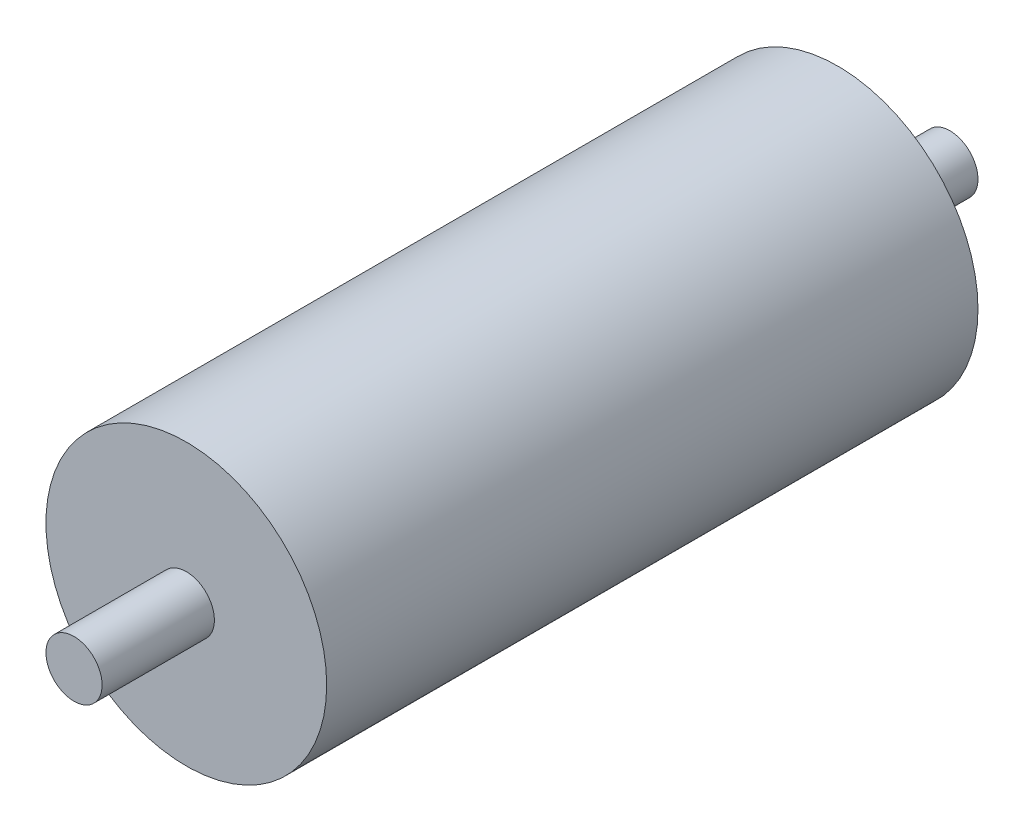
SolidWorks part; units mm, degrees
ref_plane "Front Plane" through (0, 0, 0) normal (0, 0, 1) x (1, 0, 0)
ref_plane "Top Plane" through (0, 0, 0) normal (0, 1, 0) x (1, 0, 0)
ref_plane "Right Plane" through (0, 0, 0) normal (1, 0, 0) x (0, 0, -1)
sketch "Sketch1" plane through (0, 0, 0) normal (0, 0, 1) x (1, 0, 0)
  circle A0 centre (0, 0) radius 12.5
  dimension "D1" = 25
extrude "Boss-Extrude1" add sketch "Sketch1" along normal blind 58
sketch "Sketch2" plane through (0, 0, 58) normal (0, 0, 1) x (1, 0, 0)
  circle A0 centre (0, 0) radius 2.5
  dimension "D1" = 5
extrude "Boss-Extrude2" add sketch "Sketch2" along normal blind 10
sketch "Sketch3" plane through (0, 0, 0) normal (0, 0, -1) x (-1, 0, 0)
  circle A0 centre (0, 0) radius 2.5
  dimension "D1" = 5
extrude "Boss-Extrude3" add sketch "Sketch3" along normal blind 10
